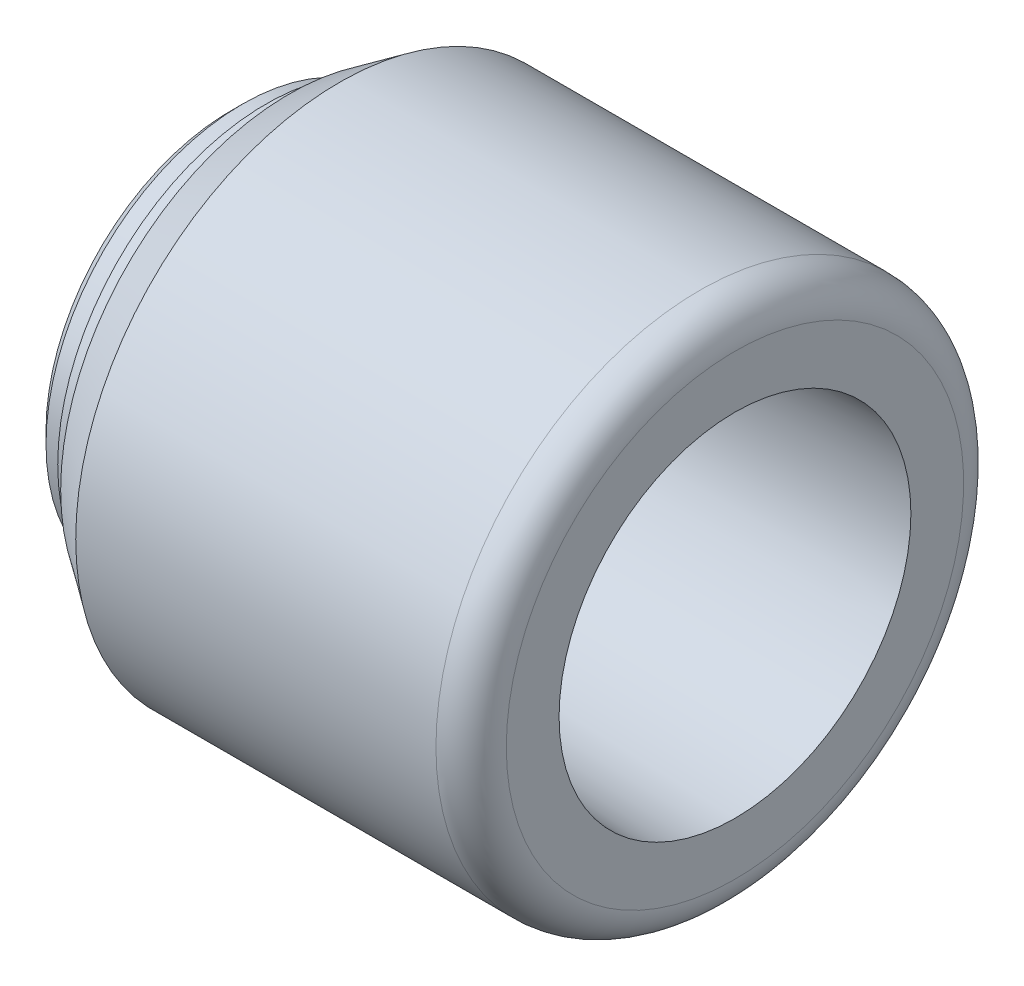
SolidWorks part; units mm, degrees
ref_plane "Plane1" through (0, 0, 0) normal (0, 0, 1) x (1, 0, 0)
ref_plane "Plane2" through (0, 0, 0) normal (0, 1, 0) x (1, 0, 0)
ref_plane "Plane3" through (0, 0, 0) normal (1, 0, 0) x (0, 0, -1)
sketch "Sketch1" plane through (0, 0, 0) normal (0, 0, 1) x (1, 0, 0)
  line L0 (0, 0) -> (80.4003, 0) construction
  line L1 (1, 16.75) -> (0, 15.75)
  line L3 (43, 15) -> (43, 19.5)
  line L4 (40, 22.5) -> (9.2844, 22.5)
  line L5 (5, 19.5) -> (5, 17.75)
  line L6 (3, 16.75) -> (1, 16.75)
  line L7 (0, 15.75) -> (0, 5.1)
  line L8 (15, 13.2497) -> (15, 5.1)
  line L9 (15.7721, 14.0492) -> (43, 15)
  line L10 (0, 5.1) -> (15, 5.1)
  line L11 (5, 19.5) -> (9.2844, 22.5)
  line L13 (5, 17.75) -> (3, 17.75)
  line L14 (3, 17.75) -> (3, 16.75)
  arc A0 (43, 19.5) -> (40, 22.5) centre (40, 19.5) ccw
  arc A1 (15, 13.2497) -> (15.7721, 14.0492) centre (15.8, 13.2497) cw
  dimension "D11" = 3
  dimension "D18" = 0.8
  dimension "D2" = 5
  dimension "D3" = 33.5
  dimension "D4" = 45
  dimension "D5" = 28
  dimension "D6" = 30
  dimension "D7" = 43
  dimension "D8" = 2
  dimension "D9" = 1
  dimension "D10" = 10.2
  dimension "D12" = 39
  dimension "D13" = 55
  dimension "D14" = 45
  dimension "D16" = 2
  dimension "D17" = 35.5
revolve "Revolve1" add sketch "Sketch1" angle 360 about L0
cosmetic thread "Cosmetic Thread1" parameters "D2"=12
